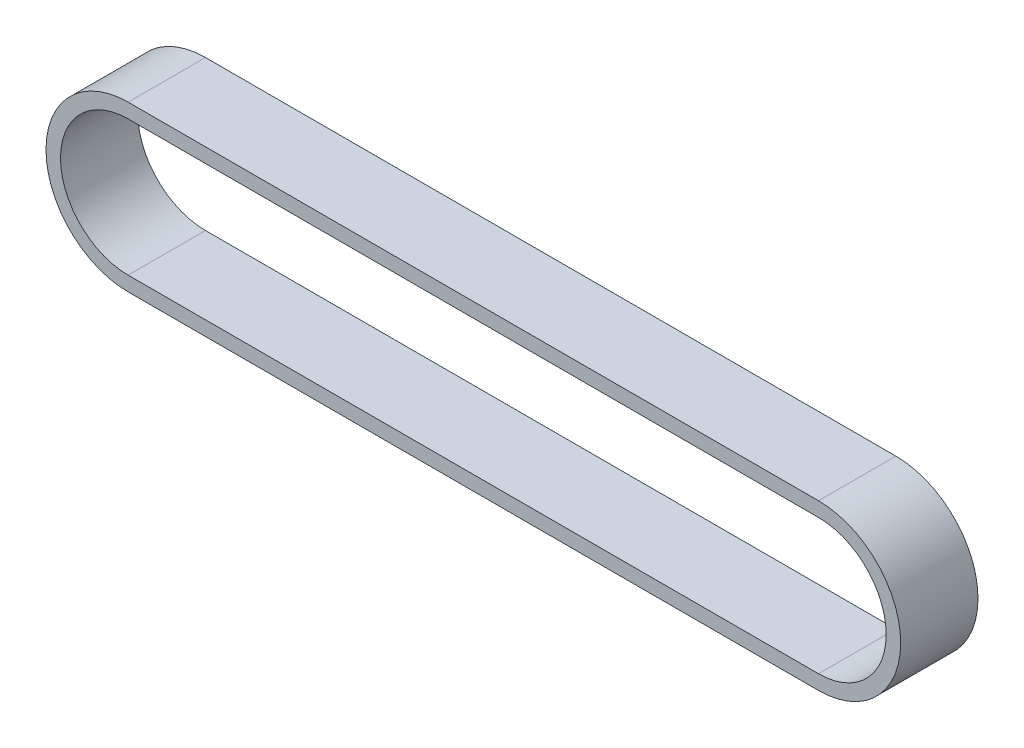
SolidWorks part; units mm, degrees
material "PF"
ref_plane "Piano frontale" through (0, 0, 0) normal (0, 0, 1) x (1, 0, 0)
ref_plane "Piano superiore" through (0, 0, 0) normal (0, 1, 0) x (1, 0, 0)
ref_plane "Piano destro" through (0, 0, 0) normal (1, 0, 0) x (0, 0, -1)
sketch "Schizzo1"
  line L0 (0, 0) -> (-57.1402, 0) construction
  line L1 (0, -5.6) -> (-57.1402, -5.6)
  line L2 (0, 5.6) -> (-57.1402, 5.6)
  line L3 (0, 0) -> (-57.1402, 0) construction
  line L4 (0, -6.8) -> (-57.1402, -6.8)
  line L5 (0, 6.8) -> (-57.1402, 6.8)
  arc A0 (0, -5.6) -> (0, 5.6) centre (0, 0) ccw
  arc A1 (-57.1402, 5.6) -> (-57.1402, -5.6) centre (-57.1402, 0) ccw
  arc A2 (0, -6.8) -> (0, 6.8) centre (0, 0) ccw
  arc A3 (-57.1402, 6.8) -> (-57.1402, -6.8) centre (-57.1402, 0) ccw
  point P3 (-28.5701, 0)
  point P8 (-28.5701, 0)
  line B0 (-57.1402, 0) -> (0, 0) construction
  dimension "D2" = 5.6
  dimension "D1" = 1.2
sketch_block_instance "puleggia piccola_2-1"
sketch_block "puleggia piccola_2"
extrude "Estrusione-Estrusione1" add sketch "Schizzo1" along normal blind 6.4
